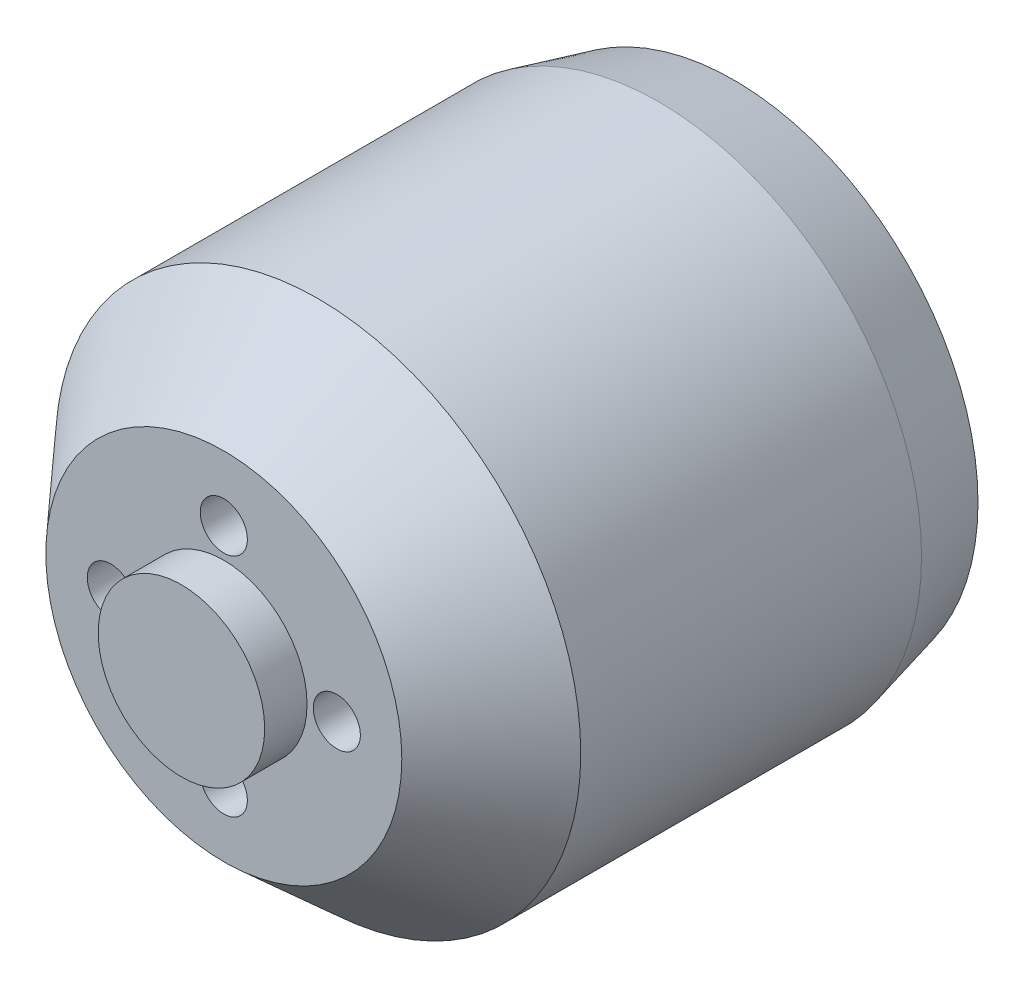
SolidWorks part; units mm, degrees
ref_plane "Front Plane" through (0, 0, 0) normal (0, 0, 1) x (1, 0, 0)
ref_plane "Top Plane" through (0, 0, 0) normal (0, 1, 0) x (1, 0, 0)
ref_plane "Right Plane" through (0, 0, 0) normal (1, 0, 0) x (0, 0, -1)
sketch "Sketch1" plane through (0, 0, 0) normal (0, 0, 1) x (1, 0, 0)
  circle A0 centre (0, 0) radius 13.95
  dimension "D1" = 27.9
extrude "Boss-Extrude1" add sketch "Sketch1" along normal blind 29.34
sketch "Sketch2" plane through (0, 0, 29.34) normal (0, 0, 1) x (1, 0, 0)
  circle A0 centre (0, 0) radius 4.42
  circle A1 centre (0, 0) radius 13.95
  circle A2 centre (0, 0) radius 13.95
  circle M2 centre (0, 0) radius 13.95
  dimension "D2" = 8.84
  dimension "D1" = 0
extrude "Cut-Extrude1" cut sketch "Sketch2" against normal blind 2.25 contours A0 M2
chamfer "Chamfer1" distance 5 distance2 4.5 1 edges at (13.95, 0, 27.09)
chamfer "Chamfer2" distance 1 distance2 4 1 edges at (13.95, 0, 0)
sketch "Sketch3" plane through (0, 0, 0) normal (0, 0, -1) x (-1, 0, 0)
  line L0 (0, 0) -> (0, 3.9853) construction
  line L1 (0, 0) -> (2.8001, 0) construction
  line L2 (0, 0) -> (8, 0) construction
  circle A0 centre (0, 9.5) radius 1.75
  circle A1 centre (8, 0) radius 1.75
  circle A2 centre (0, -9.5) radius 1.75
  circle A3 centre (-8, 0) radius 1.75
  dimension "D1" = 3.5
  dimension "D2" = 3.5
  dimension "D3" = 9.5
  dimension "D4" = 8
extrude "Cut-Extrude2" cut sketch "Sketch3" against normal blind 3 contours A1 | A3 | A2 | A0
sketch "Sketch4" plane through (0, 0, 27.09) normal (0, 0, 1) x (1, 0, 0)
  circle A0 centre (0, 6) radius 1.25
  circle A1 centre (0, 0) radius 4.42 construction
  circle A2 centre (0, 0) radius 4.42 construction
  circle A3 centre (6, 0) radius 1.25
  circle A4 centre (0, -6) radius 1.25
  circle A5 centre (-6, 0) radius 1.25
  point P14 (0, 0)
  dimension "D2" = 2.5
  dimension "D1" = 6
  dimension "D3" = 4
extrude "Cut-Extrude3" cut sketch "Sketch4" against normal blind 3
